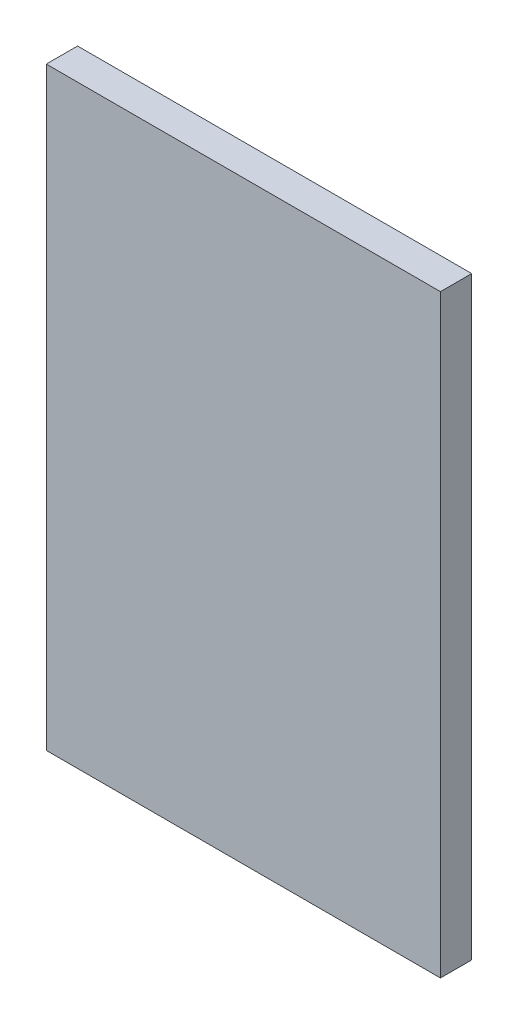
SolidWorks part; units mm, degrees
other "Markup1"
sketch "Sketch2" plane through (8.001, 12.065, 1.27) normal (0.4, 0.515, 0.7581) x (0.8844, 0, -0.4667)
material "Glass"
ref_plane "Front Plane" through (0, 0, 0) normal (0, 0, 1) x (1, 0, 0)
ref_plane "Top Plane" through (0, 0, 0) normal (0, 1, 0) x (1, 0, 0)
ref_plane "Right Plane" through (0, 0, 0) normal (1, 0, 0) x (0, 0, -1)
sketch "Sketch1" plane through (0, 0, 0) normal (0, 0, 1) x (1, 0, 0)
  line L1 (-8.001, -12.065) -> (8.001, -12.065)
  line L2 (-8.001, -12.065) -> (-8.001, 12.065)
  line L3 (-8.001, 12.065) -> (8.001, 12.065)
  line L4 (8.001, -12.065) -> (8.001, 12.065)
  line L5 (-8.001, -12.065) -> (8.001, 12.065) construction
  line L6 (-8.001, 12.065) -> (8.001, -12.065) construction
  point P0 (0, 0)
  dimension "D1" = 16.002
  dimension "D2" = 24.13
extrude "Boss-Extrude1" add sketch "Sketch1" along normal blind 1.27
